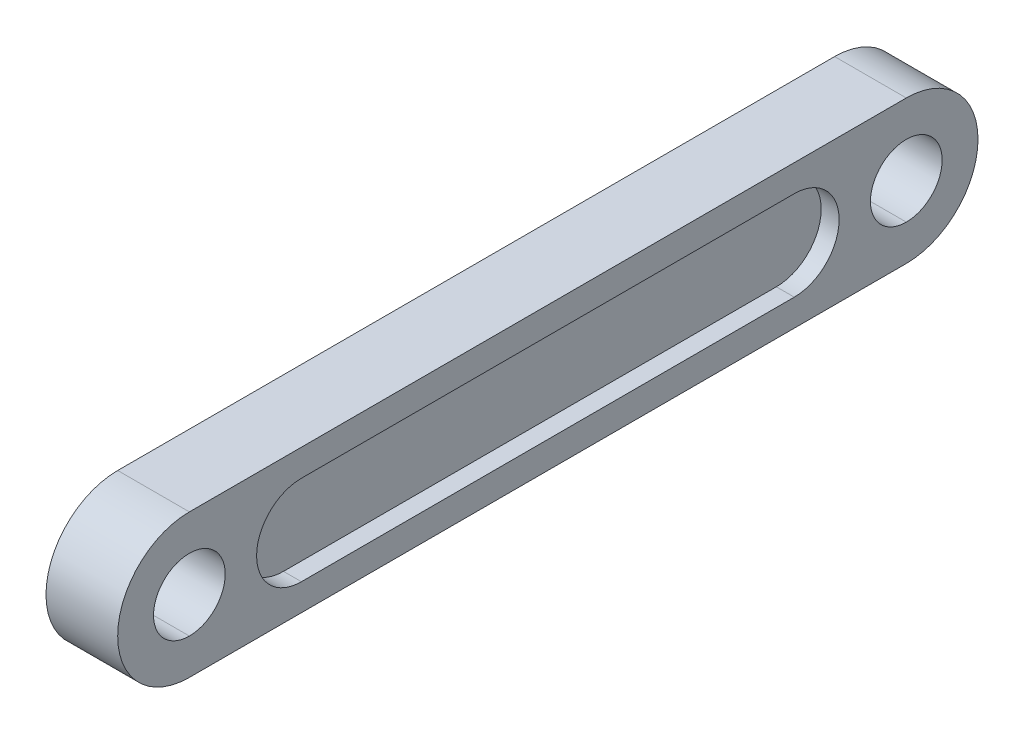
SolidWorks part; units mm, degrees
material "1.0503 (C45)"
ref_plane "前视基准面" through (0, 0, 0) normal (0, 0, 1) x (1, 0, 0)
ref_plane "上视基准面" through (0, 0, 0) normal (0, 1, 0) x (1, 0, 0)
ref_plane "右视基准面" through (0, 0, 0) normal (1, 0, 0) x (0, 0, -1)
sketch "草图1" plane through (0, 0, 0) normal (1, 0, 0) x (0, 0, -1)
  line L0 (-40, 8) -> (40, 8)
  line L1 (-40, -8) -> (40, -8)
  line L2 (0, 0) -> (0, 27.9648) construction
  line L3 (40, 0) -> (0, 0) construction
  line L4 (0, 0) -> (-40, 0) construction
  circle A0 centre (40, 0) radius 4
  arc A1 (-40, -8) -> (-40, 8) centre (-40, 0) cw
  circle A2 centre (-40, 0) radius 4
  arc A3 (40, -8) -> (40, 8) centre (40, 0) ccw
  point P4 (0, 0)
  point P6 (0, -10)
  point P7 (0, 0)
  point P14 (0, 10)
  dimension "D1" = 8
  dimension "D2" = 8
  dimension "D4" = 8
  dimension "D3" = 40
  dimension "D5" = 40
extrude "凸台-拉伸1" add sketch "草图1" along normal mid plane 8
ref_plane "基准面4" through (0, 0, -40) normal (0, 0, -1) x (-1, 0, 0)
sketch "草图5" plane through (0, 0, -40) normal (0, 0, -1) x (-1, 0, 0)
  line L0 (4, 4) -> (-4, 4)
  line L1 (-4, -4) -> (4, -4)
split line "分割线3"
ref_plane "基准面5" through (0, 0, 40) normal (0, 0, -1) x (-1, 0, 0)
sketch "草图6" plane through (0, 0, 40) normal (0, 0, -1) x (-1, 0, 0)
  line L0 (4, 4) -> (-4, 4)
  line L1 (-4, -4) -> (4, -4)
split line "分割线4"
sketch "草图7" plane through (-4, 0, 0) normal (-1, 0, 0) x (0, 0, 1)
  line L0 (-27.5, 0) -> (27.5, 0) construction
  line L1 (-27.5, 5) -> (27.5, 5)
  line L2 (-27.5, -5) -> (27.5, -5)
  arc A0 (-27.5, 5) -> (-27.5, -5) centre (-27.5, 0) ccw
  arc A1 (27.5, -5) -> (27.5, 5) centre (27.5, 0) ccw
  point P3 (0, 0)
  dimension "D2" = 5
  dimension "D1" = 55
extrude "切除-拉伸1" cut sketch "草图7" against normal blind 2
mirror "镜向1" about plane through (0, 0, 0) normal (1, 0, 0) of "切除-拉伸1"
